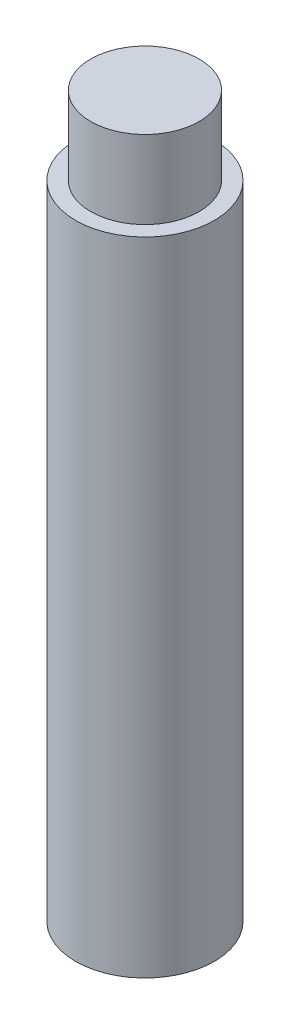
SolidWorks part; units mm, degrees
ref_plane "Front Plane" through (0, 0, 0) normal (0, 0, 1) x (1, 0, 0)
ref_plane "Top Plane" through (0, 0, 0) normal (0, 1, 0) x (1, 0, 0)
ref_plane "Right Plane" through (0, 0, 0) normal (1, 0, 0) x (0, 0, -1)
sketch "Sketch1" plane through (0, 0, 0) normal (0, 1, 0) x (1, 0, 0)
  circle A0 centre (0, 0) radius 1.6
  dimension "D1" = 3.2
extrude "Boss-Extrude1" add sketch "Sketch1" along normal mid plane 14.8
sketch "Sketch2" plane through (0, 7.4, 0) normal (0, 1, 0) x (1, 0, 0)
  circle A0 centre (0, 0) radius 1.25
  dimension "D1" = 2.5
extrude "Boss-Extrude2" add sketch "Sketch2" along normal blind 1.8
